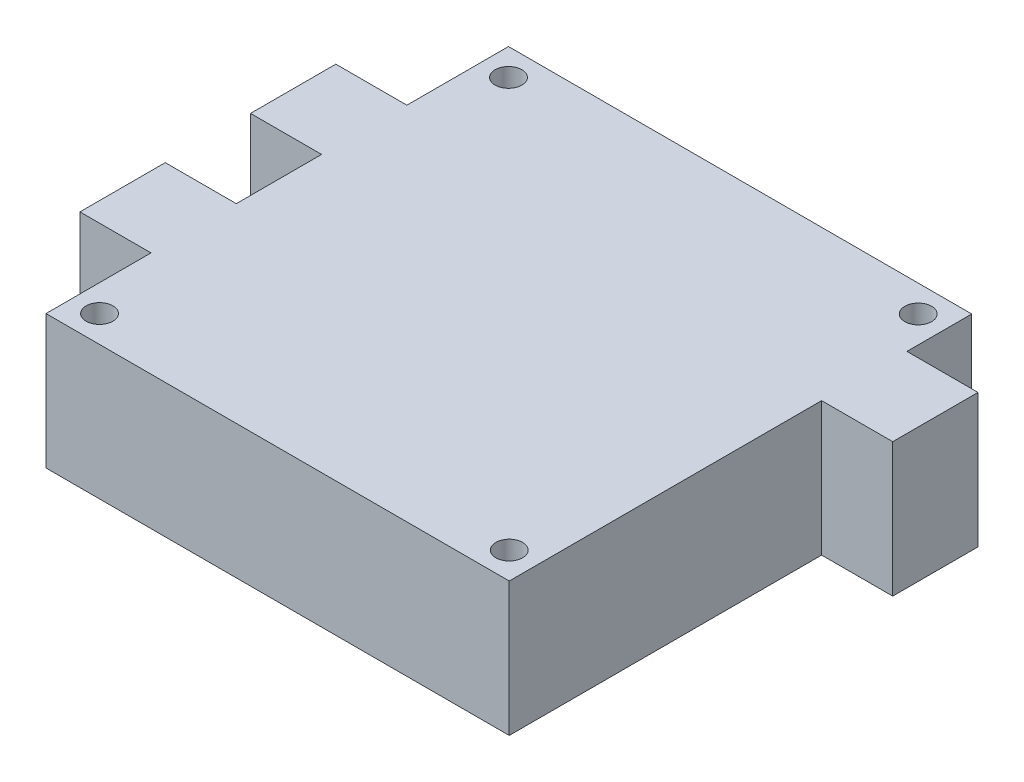
SolidWorks part; units mm, degrees
ref_plane "Front Plane" through (0, 0, 0) normal (0, 0, 1) x (1, 0, 0)
ref_plane "Top Plane" through (0, 0, 0) normal (0, 1, 0) x (1, 0, 0)
ref_plane "Right Plane" through (0, 0, 0) normal (1, 0, 0) x (0, 0, -1)
sketch "Sketch1" plane through (0, 0, 0) normal (0, 1, 0) x (1, 0, 0)
  line L0 (-27.7, 15.505) -> (-27.7, 5.305) construction
  line L1 (-27.7, 27.655) -> (27.7, 27.655)
  line L2 (-27.7, 27.655) -> (-27.7, 15.505)
  line L3 (-27.7, -27.655) -> (27.7, -27.655)
  line L4 (27.7, 27.655) -> (27.7, 19.905)
  line L5 (-27.7, 27.655) -> (27.7, -27.655) construction
  line L6 (-27.7, -27.655) -> (27.7, 27.655) construction
  line L7 (-27.7, 15.505) -> (-36.2, 15.505)
  line L8 (-27.7, 15.505) -> (-27.7, 5.305) construction
  line L9 (-27.7, 5.305) -> (-36.2, 5.305)
  line L10 (-36.2, 15.505) -> (-36.2, 5.305)
  line L11 (-27.7, -4.895) -> (-36.2, -4.895)
  line L12 (-27.7, -4.895) -> (-27.7, -15.095) construction
  line L13 (-27.7, -15.095) -> (-36.2, -15.095)
  line L14 (-36.2, -4.895) -> (-36.2, -15.095)
  line L15 (27.7, 19.905) -> (36.2, 19.905)
  line L16 (27.7, 19.905) -> (27.7, 9.705) construction
  line L17 (27.7, 9.705) -> (36.2, 9.705)
  line L18 (36.2, 19.905) -> (36.2, 9.705)
  line L19 (-27.7, 5.305) -> (-27.7, -4.895)
  line L20 (-27.7, -4.895) -> (-27.7, -15.095) construction
  line L21 (-27.7, -15.095) -> (-27.7, -27.655)
  line L22 (27.7, 19.905) -> (27.7, 9.705) construction
  line L23 (27.7, 9.705) -> (27.7, -27.655)
  circle A4 centre (-24.5, 24.455) radius 1.6
  circle A5 centre (24.5, 24.455) radius 1.6
  circle A6 centre (-24.5, -24.455) radius 1.6
  circle A7 centre (24.5, -24.455) radius 1.6
  point P0 (0, 0)
  dimension "D3" = 3.2
  dimension "D4" = 3.2
  dimension "D1" = 55.4
  dimension "D2" = 55.31
  dimension "D5" = 3.2
  dimension "D6" = 3.2
  dimension "D7" = 3.2
  dimension "D8" = 8.5
  dimension "D9" = 10.2
  dimension "D10" = 12.15
  dimension "D11" = 10.2
  dimension "D12" = 10.2
  dimension "D13" = 8.5
  dimension "D14" = 10.2
  dimension "D15" = 7.75
extrude "Boss-Extrude1" add sketch "Sketch1" along normal blind 16 contours L1 L4 L15 L18 L17 L23 L3 L21 L13 L14 L11 L19 L9 L10 L7 L2
